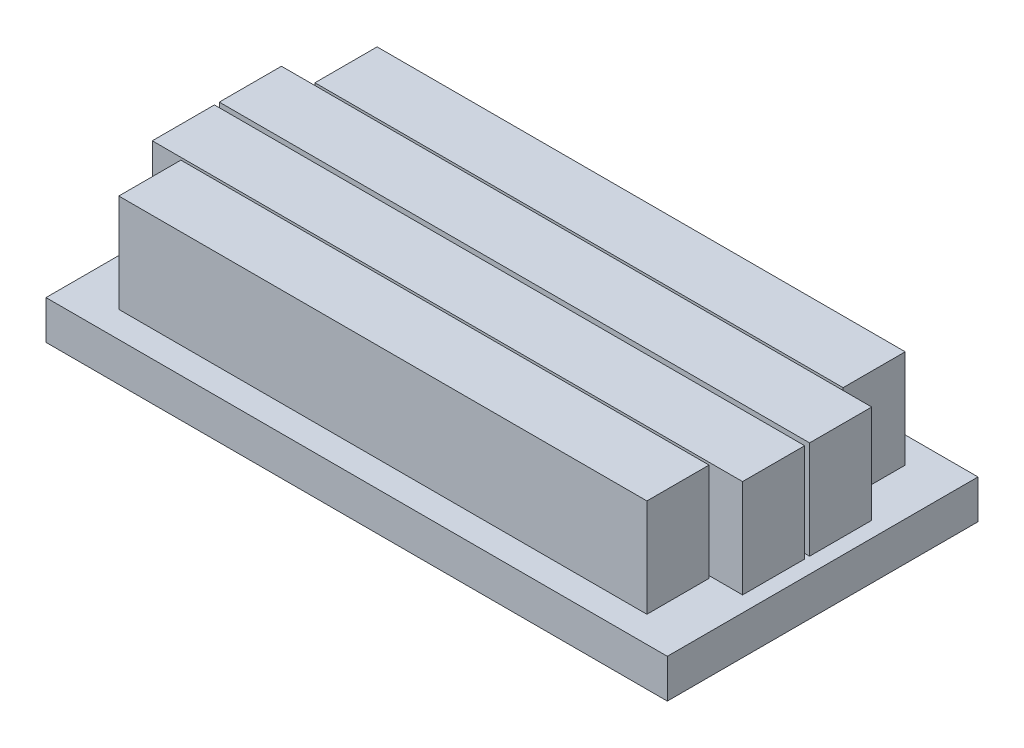
SolidWorks part; units mm, degrees
ref_plane "Front Plane" through (0, 0, 0) normal (0, 0, 1) x (1, 0, 0)
ref_plane "Top Plane" through (0, 0, 0) normal (0, 1, 0) x (1, 0, 0)
ref_plane "Right Plane" through (0, 0, 0) normal (1, 0, 0) x (0, 0, -1)
sketch "Sketch1" plane through (0, 0, 0) normal (0, 1, 0) x (1, 0, 0)
  line L0 (-12.7, -6.35) -> (12.7, -6.35)
  line L1 (-12.7, -6.35) -> (-12.7, 6.35)
  line L2 (12.7, -6.35) -> (12.7, 6.35)
  line L3 (-12.7, 6.35) -> (12.7, 6.35)
  line L4 (-12.7, -6.35) -> (12.7, 6.35) construction
  line L5 (12.7, -6.35) -> (-12.7, 6.35) construction
  point P1 (0, 0)
extrude "Boss-Extrude1" add sketch "Sketch1" along normal blind 1.5875
sketch "Sketch2" plane through (0, 1.5875, 0) normal (0, 1, 0) x (1, 0, 0)
  line L0 (-10.795, -5.28) -> (10.795, -5.28)
  line L1 (-12.065, -0.1) -> (12.065, -0.1)
  line L2 (-12.065, -0.1) -> (-12.065, -2.64)
  line L3 (-12.065, -2.64) -> (12.065, -2.64)
  line L4 (12.065, -0.1) -> (12.065, -2.64)
  line L5 (-10.795, -5.28) -> (-10.795, -2.74)
  line L6 (10.795, -5.28) -> (10.795, -2.74)
  line L7 (-10.795, -2.74) -> (10.795, -2.74)
  line L9 (10.795, -5.28) -> (-10.795, -2.74) construction
  line L10 (0, 0) -> (0, 5.3763) construction
  line L12 (12.065, -0.1) -> (-12.065, -2.64) construction
  point P4 (0, 0)
  point P7 (0, -4.01)
  point P8 (0, -1.37)
  dimension "D1" = 0.1
  dimension "D2" = 2.54
  dimension "D3" = 2.54
  dimension "D4" = 0.1
extrude "Boss-Extrude2" add sketch "Sketch2" along normal blind 4.0132
mirror "Mirror1" about plane through (0, 0, 0) normal (0, 0, 1) of "Boss-Extrude2"
